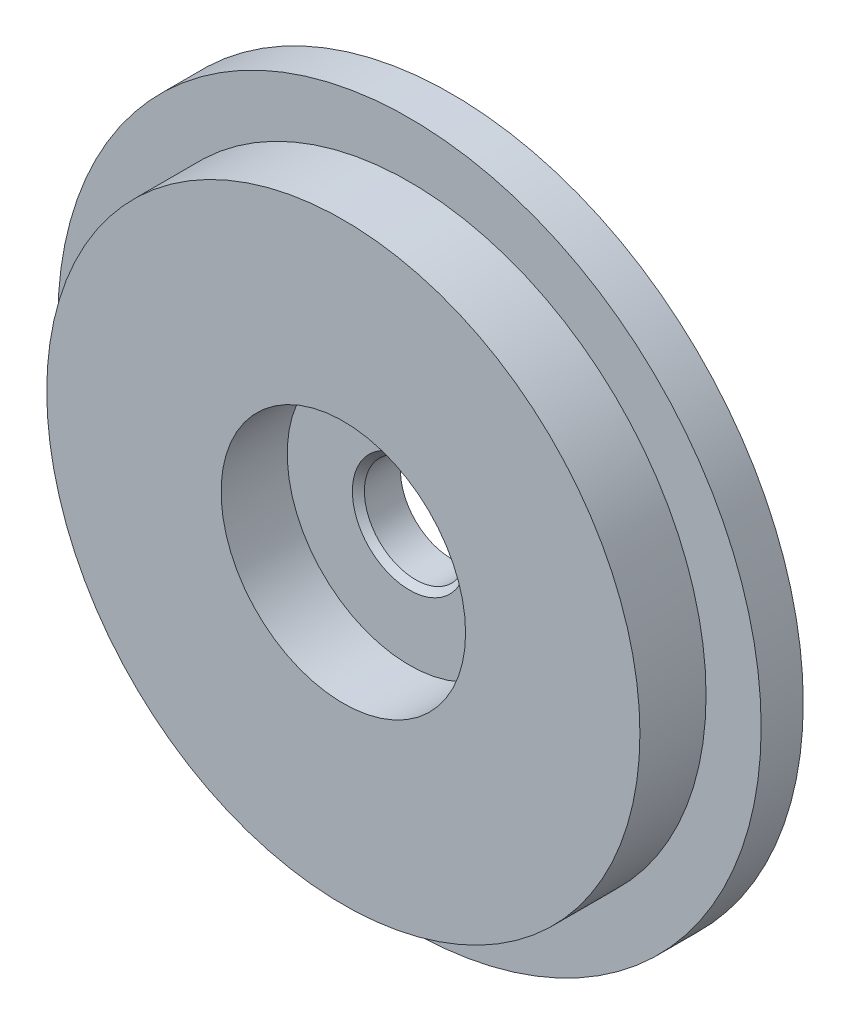
SolidWorks part; units mm, degrees
material "PA 类型 6"
ref_plane "前视基准面" through (0, 0, 0) normal (0, 0, 1) x (1, 0, 0)
ref_plane "上视基准面" through (0, 0, 0) normal (0, 1, 0) x (1, 0, 0)
ref_plane "右视基准面" through (0, 0, 0) normal (1, 0, 0) x (0, 0, -1)
sketch "草图1" plane through (0, 0, 0) normal (0, 0, 1) x (1, 0, 0)
  circle A0 centre (0, 0) radius 17.55
extrude "凸台-拉伸1" add sketch "草图1" along normal blind 2.1
sketch "草图2" plane through (0, 0, 0) normal (0, 0, 1) x (1, 0, 0)
  circle A0 centre (0, 0) radius 14.8
  circle A1 centre (0, 0) radius 6.1
extrude "凸台-拉伸2" add sketch "草图2" along normal blind 3.3 from surface at 2.1 starting at face at (17.55, 0, 2.1)
sketch "草图3" plane through (0, 0, 0) normal (0, 0, 1) x (1, 0, 0)
  circle A0 centre (0, 0) radius 2.55
extrude "切除-拉伸1" cut sketch "草图3" along normal up to next
chamfer "倒角1" distance 0.3 angle 45 1 edges at (2.55, 0, 2.1)
